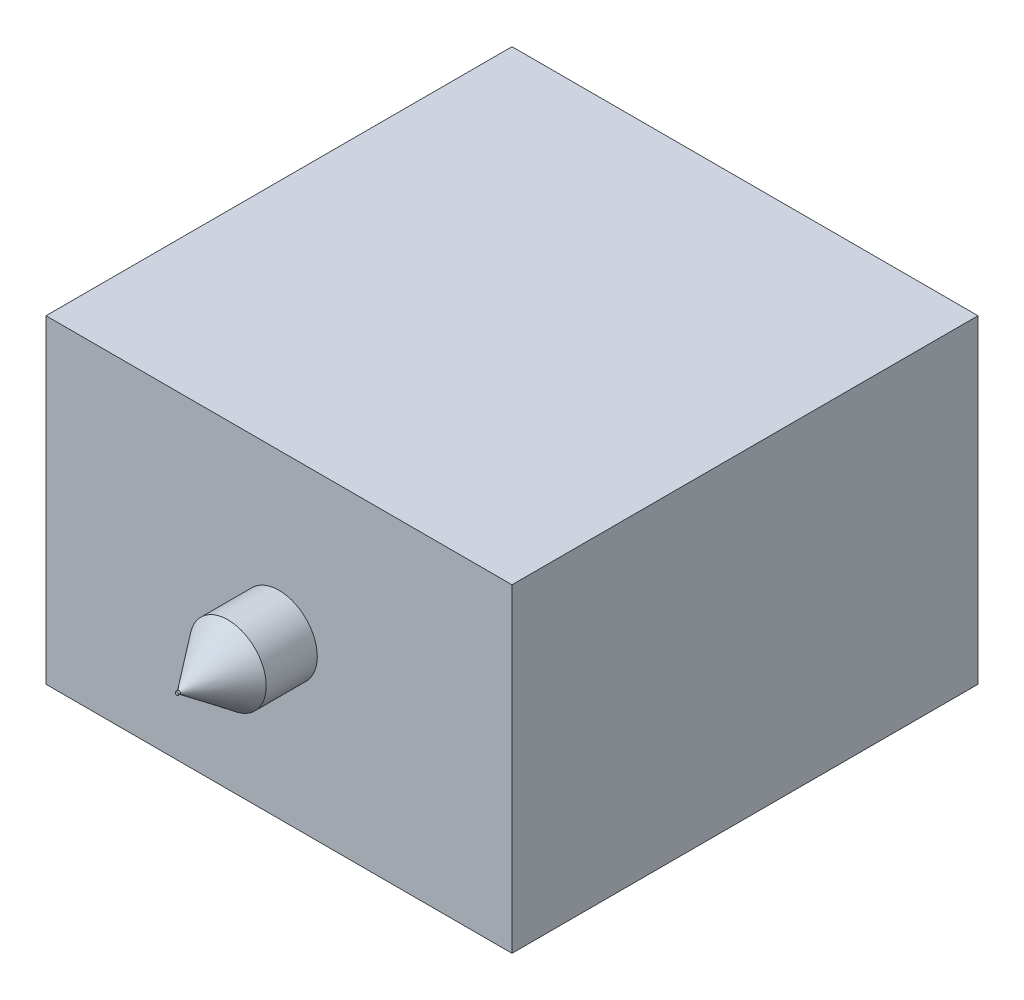
SolidWorks part; units mm, degrees
material "Acrylic (Medium-high impact)"
ref_plane "Front Plane" through (0, 0, 0) normal (0, 0, 1) x (1, 0, 0)
ref_plane "Top Plane" through (0, 0, 0) normal (0, 1, 0) x (1, 0, 0)
ref_plane "Right Plane" through (0, 0, 0) normal (1, 0, 0) x (0, 0, -1)
sketch "Sketch1" plane through (0, 0, 0) normal (0, 0, 1) x (1, 0, 0)
  line L0 (0, 152.4) -> (457.2, 152.4) construction
  line L1 (0, 0) -> (457.2, 0)
  line L2 (0, 0) -> (0, 304.8)
  line L3 (0, 304.8) -> (457.2, 304.8)
  line L4 (457.2, 0) -> (457.2, 304.8)
  line L5 (228.6, 304.8) -> (228.6, 0) construction
  dimension "D1" = 457.2
  dimension "D2" = 304.8
extrude "Chamber Base" add sketch "Sketch1" along normal blind 457.2
sketch "Sketch2" plane through (457.2, 0, 0) normal (1, 0, 0) x (0, 0, -1)
  line L1 (0, 0) -> (-457.2, 0)
  line L2 (0, 0) -> (0, 304.8)
  line L3 (0, 304.8) -> (-457.2, 304.8)
  line L4 (-457.2, 0) -> (-457.2, 304.8)
  dimension "D1" = 304.8
  dimension "D2" = 457.2
extrude "Back wall" add sketch "Sketch2" along normal blind 6.35
sketch "Sketch3" plane through (0, 304.8, 0) normal (0, 1, 0) x (1, 0, 0)
  line L0 (463.55, 0) -> (463.55, -457.2) construction
  line L1 (0, 0) -> (463.55, 0)
  line L2 (0, 0) -> (0, -457.2)
  line L3 (0, -457.2) -> (463.55, -457.2)
  line L4 (463.55, 0) -> (463.55, -457.2)
  dimension "D1" = 457.2
extrude "Side wall 2" add sketch "Sketch3" along normal blind 6.35
sketch "Sketch5" plane through (0, 0, 0) normal (0, -1, 0) x (1, 0, 0)
  line L0 (463.55, 457.2) -> (463.55, 0) construction
  line L1 (0, 0) -> (463.55, 0)
  line L2 (0, 0) -> (0, 457.2)
  line L3 (0, 457.2) -> (463.55, 457.2)
  line L4 (463.55, 0) -> (463.55, 457.2)
  dimension "D1" = 457.2
extrude "Side wall 3" add sketch "Sketch5" along normal blind 6.35
sketch "Sketch8" plane through (0, 0, 457.2) normal (0, 0, 1) x (1, 0, 0)
  line L2 (463.55, 152.4) -> (0, 152.4) construction
  line L4 (0, 311.15) -> (0, -6.35)
  line L12 (463.55, -6.35) -> (463.55, 311.15)
  line L20 (463.55, -6.35) -> (463.55, 311.15)
  line L24 (0, -6.35) -> (463.55, -6.35)
  line L25 (0, 311.15) -> (0, -6.35)
  line L26 (463.55, 311.15) -> (0, 311.15)
  line L29 (0, -6.35) -> (463.55, -6.35)
  line L30 (463.55, 311.15) -> (0, 311.15)
  dimension "D1" = 0
extrude "Top" add sketch "Sketch8" along normal blind 6.35
sketch "Sketch9" plane through (0, 0, 463.55) normal (0, 0, 1) x (1, 0, 0)
  line L0 (0, 311.15) -> (0, -6.35) construction
  line L1 (0, 152.4) -> (463.55, 152.4) construction
  line L2 (463.55, -6.35) -> (463.55, 311.15) construction
  line L3 (231.775, 311.15) -> (231.775, -6.35) construction
  line L4 (463.55, 311.15) -> (0, 311.15) construction
  line L5 (0, -6.35) -> (463.55, -6.35) construction
  circle A0 centre (231.775, 152.4) radius 38.1
  dimension "D1" = 76.2
extrude "Boss-Extrude1" add sketch "Sketch9" along normal blind 50.8
sketch "Sketch10" plane through (0, 0, 0) normal (0, 0, -1) x (-1, 0, 0)
  line L0 (-231.775, 311.15) -> (-231.775, -6.35) construction
  line L1 (-463.55, 311.15) -> (0, 311.15) construction
  line L2 (0, -6.35) -> (-463.55, -6.35) construction
  line L3 (-463.55, 152.4) -> (0, 152.4) construction
  line L4 (-463.55, -6.35) -> (-463.55, 311.15) construction
  line L5 (0, 311.15) -> (0, -6.35) construction
  circle A0 centre (-231.775, 152.4) radius 50.8
  dimension "D1" = 101.6
extrude "Boss-Extrude2" add sketch "Sketch10" along normal blind 25.4
sketch "Sketch11" plane through (0, 0, 514.35) normal (0, 0, 1) x (1, 0, 0)
  line L0 (231.775, 190.5) -> (231.775, 114.3) construction
  line L1 (193.675, 152.4) -> (269.875, 152.4) construction
  circle A0 centre (231.775, 152.4) radius 38.1 construction
  circle A1 centre (231.775, 152.4) radius 38.1 construction
  circle A2 centre (231.775, 152.4) radius 1.5875
  dimension "D1" = 3.175
extrude "Boss-Extrude3" add sketch "Sketch11" along normal blind 50.8
sketch "Sketch13" plane through (0, 0, 514.35) normal (0, 0, 1) x (1, 0, 0)
  line L0 (231.775, 190.5) -> (231.775, 152.4)
  circle A0 centre (231.775, 152.4) radius 38.1 construction
ref_plane "Plane2" through (231.775, 0, 0) normal (-1, 0, 0) x (0, 0, 1)
sketch "Sketch15" plane through (231.775, 0, 0) normal (-1, 0, 0) x (0, 0, 1)
  line L3 (514.35, 190.5) -> (514.35, 152.4)
  line L4 (514.35, 114.3) -> (514.35, 190.5) construction
  line L5 (514.35, 152.4) -> (565.15, 152.4)
  line L6 (565.15, 150.8125) -> (565.15, 153.9875) construction
  line L7 (565.15, 152.4) -> (514.35, 190.5)
revolve "Revolve1" add sketch "Sketch15" angle 360 about L5
